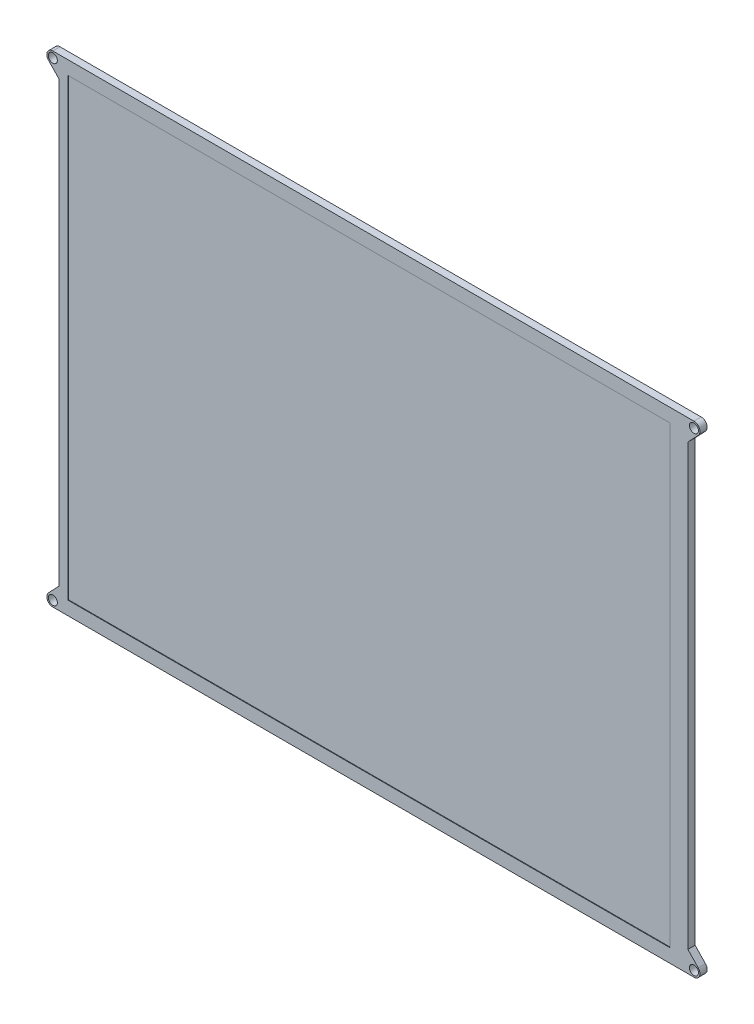
SolidWorks part; units mm, degrees
ref_plane "Alzado" through (0, 0, 0) normal (0, 0, 1) x (1, 0, 0)
ref_plane "Planta" through (0, 0, 0) normal (0, 1, 0) x (1, 0, 0)
ref_plane "Vista lateral" through (0, 0, 0) normal (1, 0, 0) x (0, 0, -1)
sketch "Croquis1" plane through (0, 0, 0) normal (0, 0, 1) x (1, 0, 0)
  line L0 (104.5, 80) -> (106.5, 80)
  line L1 (-104.5, 80) -> (104.5, 80)
  line L2 (-104.5, 80) -> (-104.5, -80)
  line L3 (-104.5, -80) -> (104.5, -80)
  line L4 (104.5, 80) -> (104.5, -80)
  line L5 (-104.5, 80) -> (104.5, -80) construction
  line L6 (-104.5, -80) -> (104.5, 80) construction
  line L7 (106.5, 78) -> (108.5, 78) construction
  line L8 (104.5, 80) -> (104.5, 73)
  line L9 (104.5, 73) -> (107.9483, 76.6207)
  line L10 (-106.5, 78) -> (-108.5, 78) construction
  line L11 (-104.5, 73) -> (-107.9483, 76.6207)
  line L12 (-104.5, 80) -> (-104.5, 73)
  line L13 (0, 80) -> (0, 78) construction
  line L14 (-106.5, 78) -> (106.5, 78) construction
  line L15 (-104.5, 80) -> (-106.5, 80)
  line L16 (-104.5, 0) -> (104.5, 0) construction
  line L17 (106.5, -78) -> (108.5, -78) construction
  line L18 (104.5, -73) -> (107.9483, -76.6207)
  line L19 (104.5, -80) -> (104.5, -73)
  line L20 (104.5, -80) -> (106.5, -80)
  line L21 (-106.5, -78) -> (-108.5, -78) construction
  line L22 (-104.5, -80) -> (-106.5, -80)
  line L23 (-104.5, -80) -> (-104.5, -73)
  line L24 (-104.5, -73) -> (-107.9483, -76.6207)
  circle A1 centre (106.5, 78) radius 1.5
  arc A3 (107.9483, 76.6207) -> (106.5, 80) centre (106.5, 78) ccw
  arc A4 (-107.9483, 76.6207) -> (-106.5, 80) centre (-106.5, 78) cw
  circle A5 centre (-106.5, 78) radius 1.5
  arc A6 (107.9483, -76.6207) -> (106.5, -80) centre (106.5, -78) cw
  circle A7 centre (106.5, -78) radius 1.5
  circle A8 centre (-106.5, -78) radius 1.5
  arc A9 (-107.9483, -76.6207) -> (-106.5, -80) centre (-106.5, -78) ccw
  point P0 (0, 0)
  point P7 (104.5, 79)
  point P8 (108.5, 79)
  point P9 (105.5, 80)
  point P10 (105.5, -80)
  point P51 (0, 78)
  dimension "D1" = 209
  dimension "D2" = 160
extrude "Saliente-Extruir1" add sketch "Croquis1" along normal blind 2.4 contours L4 L1 L2 L3 | A4 L11 L2 L15 A5 | L9 A3 L0 L4 A1 | A6 L18 L4 L20 A7 | L24 A9 L22 L2 A8
sketch "Croquis2" plane through (0, 0, 2.4) normal (0, 0, 1) x (1, 0, 0)
  line L0 (104.5, 0) -> (98.5, 0) construction
  line L1 (-101.5, 75.5) -> (98.5, 75.5)
  line L2 (-101.5, 75.5) -> (-101.5, -75.5)
  line L3 (-101.5, -75.5) -> (98.5, -75.5)
  line L4 (98.5, 75.5) -> (98.5, -75.5)
  line L5 (-101.5, 75.5) -> (98.5, -75.5) construction
  line L6 (-101.5, -75.5) -> (98.5, 75.5) construction
  line L7 (104.5, 73) -> (104.5, -73) construction
  point P0 (-1.5, 0)
  dimension "D1" = 200
  dimension "D2" = 151
  dimension "D3" = 6
extrude "Cortar-Extruir1" cut sketch "Croquis2" against normal blind 0.2
